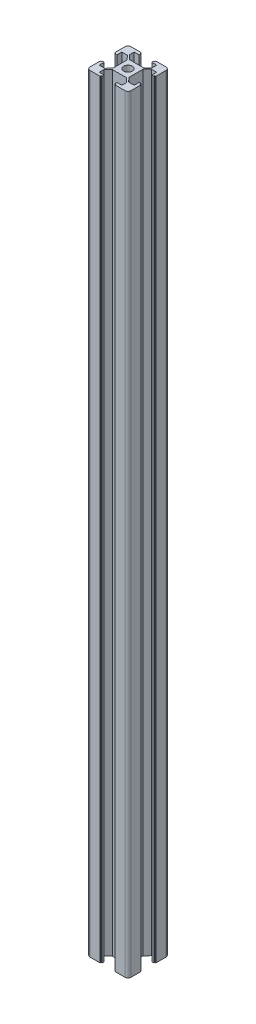
SolidWorks part; units mm, degrees
material "6063-T5"
ref_plane "Front Plane" through (0, 0, 0) normal (0, 0, 1) x (1, 0, 0)
ref_plane "Top Plane" through (0, 0, 0) normal (0, 1, 0) x (1, 0, 0)
ref_plane "Right Plane" through (0, 0, 0) normal (1, 0, 0) x (0, 0, -1)
sketch "Sketch1" plane through (0, 0, 0) normal (0, 1, 0) x (1, 0, 0)
  line L0 (0, 10) -> (6.1, 10) construction
  line L3 (1.5, 20) -> (6.4, 20)
  line L5 (13.5, 5.8345) -> (6.5, 5.8345)
  line L6 (13.9, 6.5) -> (13.9, 13.5)
  line L7 (13.5, 14.1655) -> (6.5, 14.1655)
  line L8 (6.1, 6.5) -> (6.1, 13.5)
  line L9 (13.8307, 6.0319) -> (6.1693, 13.9681) construction
  line L10 (13.8307, 13.9681) -> (6.1693, 6.0319) construction
  line L11 (13.9, 10) -> (20, 10) construction
  line L12 (10, 20) -> (10, 13.9) construction
  line L13 (10, 6.1) -> (10, 0) construction
  line L14 (4.5, 18.5) -> (4.5, 16.2373)
  line L15 (6.9, 18.5) -> (6.9, 19.5)
  line L16 (6.5, 14.1655) -> (4.5, 16.2373)
  line L17 (6.1, 13.5) -> (4.1693, 15.5)
  line L18 (1.5, 15.5) -> (4.1693, 15.5)
  line L19 (1.5, 15.5) -> (1.5, 13.1)
  line L20 (4.5, 18.5) -> (6.9, 18.5)
  line L21 (1.5, 13.1) -> (0.5, 13.1)
  line L22 (0, 13.6) -> (0, 18.5)
  line L23 (20, 13.6) -> (20, 18.5)
  line L24 (18.5, 13.1) -> (19.5, 13.1)
  line L25 (15.5, 18.5) -> (13.1, 18.5)
  line L26 (18.5, 15.5) -> (18.5, 13.1)
  line L27 (18.5, 15.5) -> (15.8307, 15.5)
  line L28 (13.9, 13.5) -> (15.8307, 15.5)
  line L29 (13.5, 14.1655) -> (15.5, 16.2373)
  line L30 (13.1, 18.5) -> (13.1, 19.5)
  line L31 (15.5, 18.5) -> (15.5, 16.2373)
  line L32 (18.5, 20) -> (13.6, 20)
  line L33 (0, 13.6) -> (0.5, 13.6)
  line L34 (0.5, 13.6) -> (0.5, 13.1)
  line L35 (6.4, 20) -> (6.4, 19.5)
  line L36 (6.4, 19.5) -> (6.9, 19.5)
  line L37 (0.5, 6.4) -> (0.5, 6.9)
  line L38 (0, 6.4) -> (0.5, 6.4)
  line L39 (6.4, 0.5) -> (6.9, 0.5)
  line L40 (6.4, 0) -> (6.4, 0.5)
  line L41 (13.6, 0) -> (13.6, 0.5)
  line L42 (13.6, 0.5) -> (13.1, 0.5)
  line L43 (13.6, 19.5) -> (13.1, 19.5)
  line L44 (13.6, 20) -> (13.6, 19.5)
  line L45 (20, 6.4) -> (19.5, 6.4)
  line L46 (19.5, 6.4) -> (19.5, 6.9)
  line L47 (19.5, 13.6) -> (19.5, 13.1)
  line L49 (20, 13.6) -> (19.5, 13.6)
  line L90 (10, 0) -> (10, 6.1) construction
  line L91 (18.5, 0) -> (13.6, 0)
  line L93 (15.5, 1.5) -> (15.5, 3.7627)
  line L94 (13.1, 1.5) -> (13.1, 0.5)
  line L95 (13.5, 5.8345) -> (15.5, 3.7627)
  line L96 (13.9, 6.5) -> (15.8307, 4.5)
  line L97 (18.5, 4.5) -> (15.8307, 4.5)
  line L98 (18.5, 4.5) -> (18.5, 6.9)
  line L99 (15.5, 1.5) -> (13.1, 1.5)
  line L100 (18.5, 6.9) -> (19.5, 6.9)
  line L101 (20, 6.4) -> (20, 1.5)
  line L102 (4.5, 1.5) -> (6.9, 1.5)
  line L103 (1.5, 4.5) -> (1.5, 6.9)
  line L104 (1.5, 4.5) -> (4.1693, 4.5)
  line L105 (6.1, 6.5) -> (4.1693, 4.5)
  line L106 (6.5, 5.8345) -> (4.5, 3.7627)
  line L107 (6.9, 1.5) -> (6.9, 0.5)
  line L108 (4.5, 1.5) -> (4.5, 3.7627)
  line L138 (0, 6.4) -> (0, 1.5)
  line L139 (1.5, 6.9) -> (0.5, 6.9)
  line L147 (1.5, 0) -> (6.4, 0)
  circle A0 centre (10, 10) radius 2
  arc A1 (0, 18.5) -> (1.5, 20) centre (1.5, 18.5) cw
  arc A2 (20, 18.5) -> (18.5, 20) centre (18.5, 18.5) ccw
  arc A3 (18.5, 0) -> (20, 1.5) centre (18.5, 1.5) ccw
  arc A4 (1.5, 0) -> (0, 1.5) centre (1.5, 1.5) cw
  point P5 (10, 10)
  dimension "D3" = 4
  dimension "D2" = 1.5
  dimension "D4" = 6.1
  dimension "D5" = 0.75
  dimension "D6" = 11
  dimension "D7" = 11
  dimension "D8" = 6.2
  dimension "D9" = 20
  dimension "D10" = 6.2
  dimension "D11" = 1.5
  dimension "D12" = 20
  dimension "D13" = 7
  dimension "D14" = 7.2
  dimension "D15" = 7.2
  dimension "D16" = 0.5
  dimension "D17" = 0.5
extrude "Boss-Extrude1" add sketch "Sketch1" along normal blind 374
hole_wizard "M5 Tapped Hole1" positions "Sketch2" profile "Sketch3" tap size "M5" standard "DIN"
sketch "Sketch2" plane through (0, 374, 0) normal (0, 1, 0) x (1, 0, 0)
  point P0 (10, 10)
cosmetic thread "Hole Thread1" parameters "D1"=9.2, "D2"=5
sketch "Sketch3" plane through (10, 374, -10) normal (1, 0, 0) x (0, 0, 1)
  line L0 (0, 0) -> (0, 11.2618)
  line L1 (0, 11.2618) -> (2.1, 10)
  line L2 (2.1, 10) -> (2.1, 0)
  line L5 (2.1, 0) -> (0, 0)
  line L10 (0, 11.2618) -> (-2.1, 10) construction
  line L11 (0, -6.35) -> (0, 107.95) construction
  dimension "Tap Drill Dia." = 4.2
  dimension "Tap Drill Depth" = 10
  dimension "Drill Angle" = 118
hole_wizard "M5 Tapped Hole2" positions "Sketch4" profile "Sketch5" tap size "M5" standard "DIN"
sketch "Sketch4" plane through (0, 0, 0) normal (0, -1, 0) x (-1, 0, 0)
  point P0 (-10, 10)
sketch "Sketch5" plane through (10, 0, -10) normal (1, 0, 0) x (0, 0, -1)
  line L0 (0, 0) -> (0, 12.8618)
  line L1 (0, 12.8618) -> (2.1, 11.6)
  line L2 (2.1, 11.6) -> (2.1, 0)
  line L5 (2.1, 0) -> (0, 0)
  line L10 (0, 12.8618) -> (-2.1, 11.6) construction
  line L11 (0, -6.35) -> (0, 107.95) construction
  dimension "Tap Drill Dia." = 4.2
  dimension "Tap Drill Depth" = 11.6
  dimension "Drill Angle" = 118
cosmetic thread "Hole Thread2" parameters "D1"=9.2, "D2"=5
